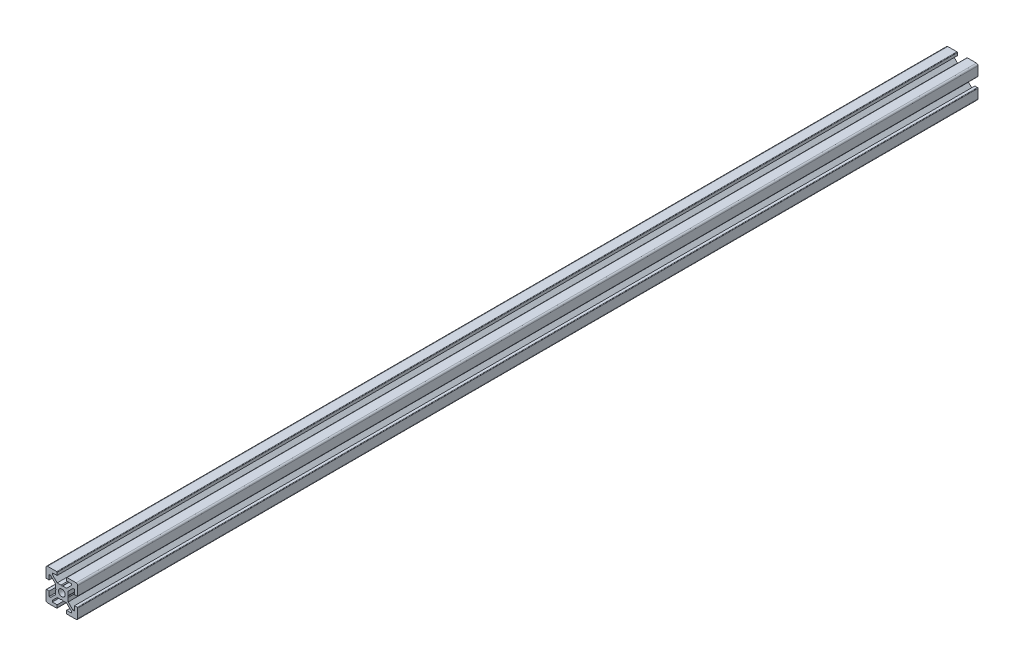
SolidWorks part; units mm, degrees
material "6063-T5"
ref_plane "Front Plane" through (0, 0, 0) normal (0, 0, 1) x (1, 0, 0)
ref_plane "Top Plane" through (0, 0, 0) normal (0, 1, 0) x (1, 0, 0)
ref_plane "Right Plane" through (0, 0, 0) normal (1, 0, 0) x (0, 0, -1)
ref_plane "Plane1" through (0, 0, 0) normal (0, 0, 1) x (1, 0, 0)
sketch "Sketch1" plane through (0, 0, 0) normal (0, 0, 1) x (1, 0, 0)
  line L0 (-10, 9) -> (-10, 3.3)
  line L1 (-9.7, 3) -> (-8, 3)
  line L2 (-8, 3) -> (-8, 6)
  line L3 (-8, 6) -> (-7.0607, 6)
  line L4 (-7.0607, 6) -> (-4, 2.9393)
  line L5 (-4, 2.9393) -> (-4, 0.5196)
  line L6 (-4, 0.5196) -> (-3.7, 0)
  line L7 (-3.7, 0) -> (-4, -0.5196)
  line L8 (-4, -0.5196) -> (-4, -2.9393)
  line L9 (-4, -2.9393) -> (-7.0607, -6)
  line L10 (-7.0607, -6) -> (-8, -6)
  line L11 (-8, -6) -> (-8, -3)
  line L12 (-8, -3) -> (-9.7, -3)
  line L13 (-10, -3.3) -> (-10, -9)
  line L14 (-9, -10) -> (-3.3, -10)
  line L15 (-3, -9.7) -> (-3, -8)
  line L16 (-3, -8) -> (-6, -8)
  line L17 (-6, -8) -> (-6, -7.0607)
  line L18 (-6, -7.0607) -> (-2.9393, -4)
  line L19 (-2.9393, -4) -> (-0.5196, -4)
  line L20 (-0.5196, -4) -> (0, -3.7)
  line L21 (0, -3.7) -> (0.5196, -4)
  line L22 (0.5196, -4) -> (2.9393, -4)
  line L23 (2.9393, -4) -> (6, -7.0607)
  line L24 (6, -7.0607) -> (6, -8)
  line L25 (6, -8) -> (3, -8)
  line L26 (3, -8) -> (3, -9.7)
  line L27 (3.3, -10) -> (9, -10)
  line L28 (10, -9) -> (10, -3.3)
  line L29 (9.7, -3) -> (8, -3)
  line L30 (8, -3) -> (8, -6)
  line L31 (8, -6) -> (7.0606, -6)
  line L32 (7.0606, -6) -> (4, -2.9393)
  line L33 (4, -2.9393) -> (4, -0.5196)
  line L34 (4, -0.5196) -> (3.7, 0)
  line L35 (3.7, 0) -> (4, 0.5196)
  line L36 (4, 0.5196) -> (4, 2.9393)
  line L37 (4, 2.9393) -> (7.0607, 6)
  line L38 (7.0607, 6) -> (8, 6)
  line L39 (8, 6) -> (8, 3)
  line L40 (8, 3) -> (9.7, 3)
  line L41 (10, 3.3) -> (10, 9)
  line L42 (9, 10) -> (3.3, 10)
  line L43 (3, 9.7) -> (3, 8)
  line L44 (3, 8) -> (6, 8)
  line L45 (6, 8) -> (6, 7.0607)
  line L46 (6, 7.0607) -> (2.9393, 4)
  line L47 (2.9393, 4) -> (0.5196, 4)
  line L48 (0.5196, 4) -> (0, 3.7)
  line L49 (0, 3.7) -> (-0.5196, 4)
  line L50 (-0.5196, 4) -> (-2.9394, 4)
  line L51 (-2.9394, 4) -> (-6, 7.0606)
  line L52 (-6, 7.0606) -> (-6, 8)
  line L53 (-6, 8) -> (-3, 8)
  line L54 (-3, 8) -> (-3, 9.7)
  line L55 (-3.3, 10) -> (-9, 10)
  arc A0 (-10, 3.3) -> (-9.7, 3) centre (-9.7, 3.3) ccw
  arc A1 (-9.7, -3) -> (-10, -3.3) centre (-9.7, -3.3) ccw
  arc A2 (-10, -9) -> (-9, -10) centre (-9, -9) ccw
  arc A3 (-3.3, -10) -> (-3, -9.7) centre (-3.3, -9.7) ccw
  arc A4 (3, -9.7) -> (3.3, -10) centre (3.3, -9.7) ccw
  arc A5 (9, -10) -> (10, -9) centre (9, -9) ccw
  arc A6 (10, -3.3) -> (9.7, -3) centre (9.7, -3.3) ccw
  arc A7 (9.7, 3) -> (10, 3.3) centre (9.7, 3.3) ccw
  arc A8 (10, 9) -> (9, 10) centre (9, 9) ccw
  arc A9 (3.3, 10) -> (3, 9.7) centre (3.3, 9.7) ccw
  arc A10 (-3, 9.7) -> (-3.3, 10) centre (-3.3, 9.7) ccw
  arc A11 (-9, 10) -> (-10, 9) centre (-9, 9) ccw
extrude "Boss-Extrude1" add sketch "Sketch1" against normal blind 567.5
ref_plane "Plane2" through (0, 0, 0) normal (1, 0, 0) x (0, 0, -1)
sketch "Sketch2" plane through (0, 0, 0) normal (1, 0, 0) x (0, 0, -1)
  line L0 (0, 0) -> (0, 2.1)
  line L1 (0, 2.1) -> (567.5, 2.1)
  line L2 (567.5, 2.1) -> (567.5, 0)
  line L3 (567.5, 0) -> (0, 0)
  line L4 (567.5, 0) -> (0, 0) construction
  dimension "D1" = 2.1
  dimension "D2" = 567.5
revolve "Cut-Revolve1" cut sketch "Sketch2" angle 360 about L4
ref_plane "Plane3" through (0, 0, -283.75) normal (0, 0, 1) x (1, 0, 0)
sketch "Sketch4" plane through (4, 0, 0) normal (1, 0, 0) x (0, 0, -1)
  line L0 (567.5, 0) -> (0, 0) construction
  line L1 (0, -2.9393) -> (0, -0.5196) construction
  line L2 (283.75, 2.9393) -> (283.75, -2.9393) construction
  line L3 (567.5, 2.9393) -> (0, 2.9393) construction
  line L4 (567.5, -2.9393) -> (0, -2.9393) construction
  circle A0 centre (10, 0) radius 2.5
  circle A1 centre (557.5, 0) radius 2.5
  dimension "D1" = 5
  dimension "D2" = 10
extrude "Cut-Extrude1" cut sketch "Sketch4" against normal up to surface (8 mm away) up to face at (-4, 1.7295, -283.75)
